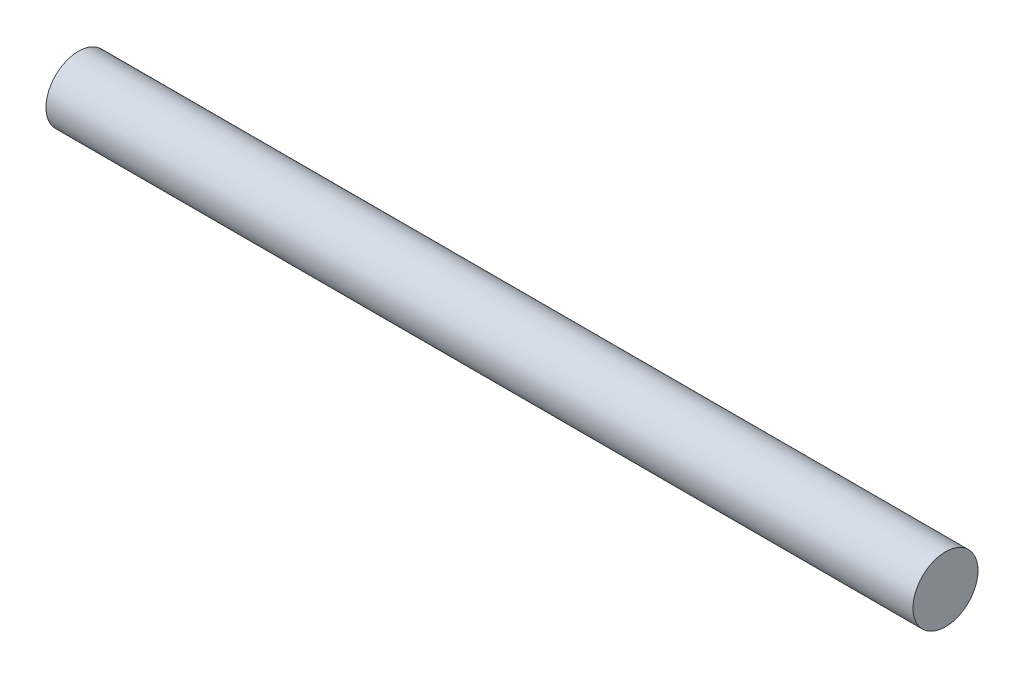
SolidWorks part; units mm, degrees
ref_plane "Front Plane" through (0, 0, 0) normal (0, 0, 1) x (1, 0, 0)
ref_plane "Top Plane" through (0, 0, 0) normal (0, 1, 0) x (1, 0, 0)
ref_plane "Right Plane" through (0, 0, 0) normal (1, 0, 0) x (0, 0, -1)
sketch "Sketch1" plane through (0, 0, 0) normal (1, 0, 0) x (0, 0, -1)
  circle A0 centre (0, 0) radius 1.5
extrude "Boss-Extrude1" add sketch "Sketch1" along normal blind 40
